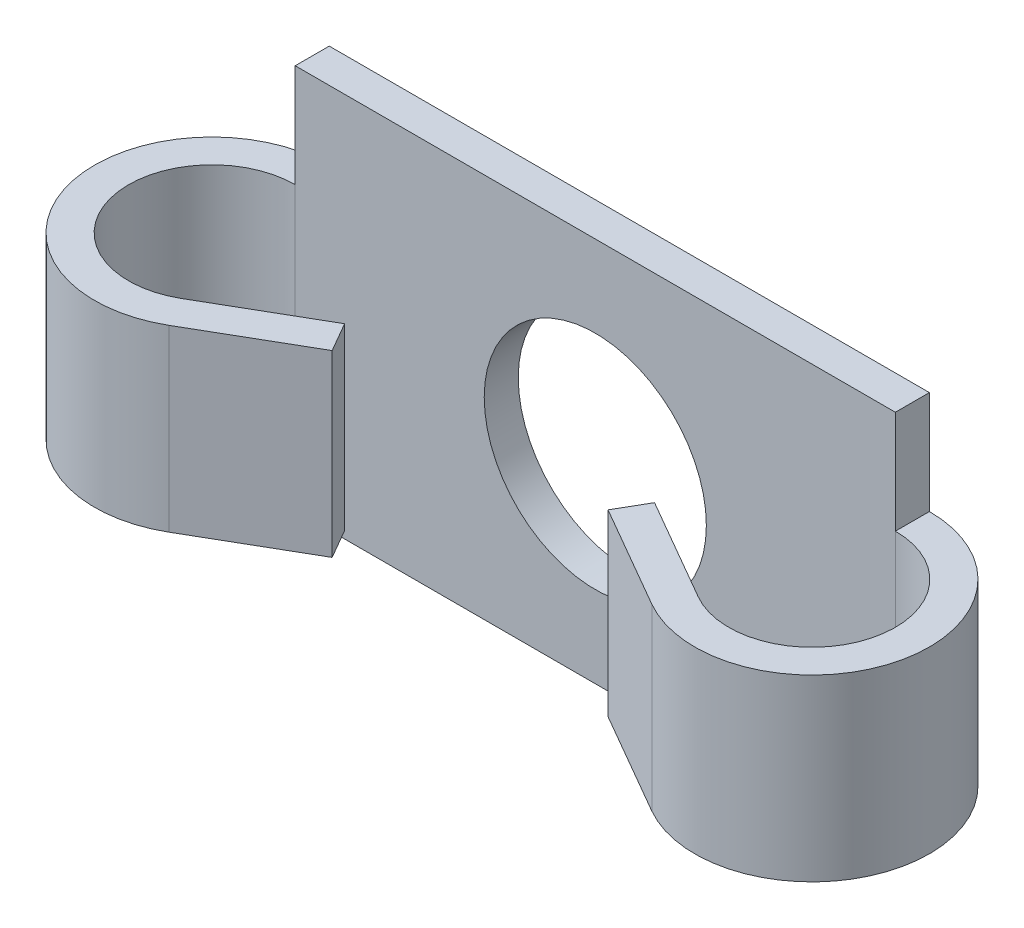
SolidWorks part; units mm, degrees
ref_plane "Спереди" through (0, 0, 0) normal (0, 0, 1) x (1, 0, 0)
ref_plane "Сверху" through (0, 0, 0) normal (0, 1, 0) x (1, 0, 0)
ref_plane "Справа" through (0, 0, 0) normal (1, 0, 0) x (0, 0, -1)
sketch "Эскиз1" plane through (0, 0, 0) normal (0, 0, 1) x (1, 0, 0)
  line L1 (-16.75, -10.75) -> (16.75, -10.75)
  line L2 (-16.75, -10.75) -> (-16.75, 10.75)
  line L3 (-16.75, 10.75) -> (16.75, 10.75)
  line L4 (16.75, -10.75) -> (16.75, 10.75)
  line L5 (-16.75, -10.75) -> (16.75, 10.75) construction
  line L6 (-16.75, 10.75) -> (16.75, -10.75) construction
  circle A0 centre (0, 0) radius 6.2
  point P0 (0, 0)
  dimension "D3" = 12.4
  dimension "D1" = 33.5
  dimension "D2" = 21.5
extrude "Бобышка-Вытянуть1" add sketch "Эскиз1" along normal blind 1.9
sketch "Эскиз3" plane through (0, 0, 0) normal (0, 1, 0) x (1, 0, 0)
  line L0 (16.75, -1.9) -> (-16.75, -1.9) construction
  line L1 (16.75, 0) -> (-16.75, 0) construction
  line L2 (-14.425, -10.577) -> (-8.65, -7.2428)
  line L3 (-8.65, -7.2428) -> (-7.7, -8.8883)
  line L4 (-7.7, -8.8883) -> (-13.475, -12.2225)
  line L5 (-16.75, -11.2) -> (-16.75, 0) construction
  line L6 (-6.2, 0) -> (-6.2, -1.9) construction
  line L7 (-16.75, -1.9) -> (-16.75, 0)
  arc A0 (-16.75, -1.9) -> (-14.425, -10.577) centre (-16.75, -6.55) ccw
  arc A1 (-16.75, 0) -> (-13.475, -12.2225) centre (-16.75, -6.55) ccw
  dimension "D1" = 11.2
  dimension "D2" = 30
  dimension "D3" = 1.5
extrude "Бобышка-Вытянуть2" add sketch "Эскиз3" along normal mid plane 10
mirror "Зеркальное отражение1" about plane through (0, 0, 0) normal (1, 0, 0) of "Бобышка-Вытянуть2"
